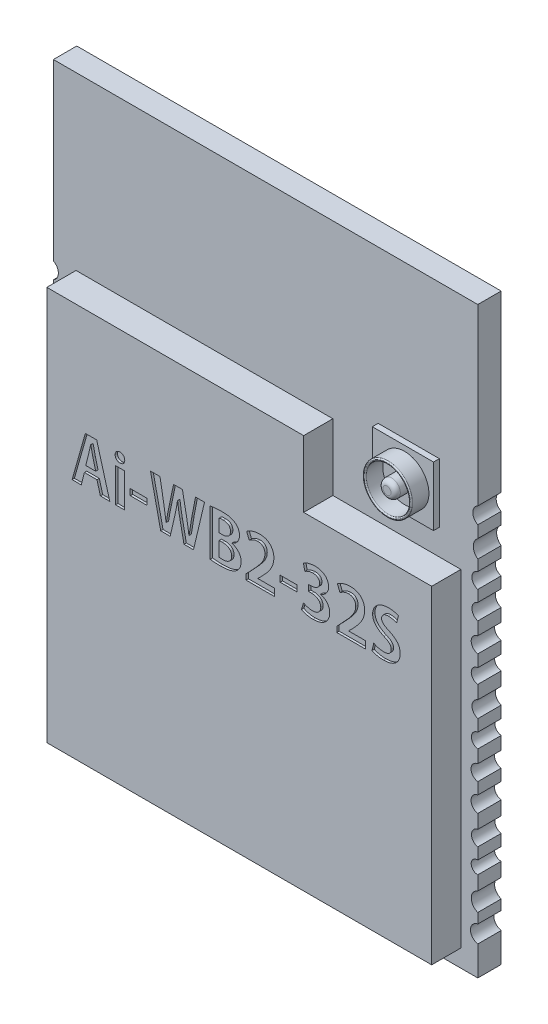
SolidWorks part; units mm, degrees
ref_plane "Plan de face" through (0, 0, 0) normal (0, 0, 1) x (1, 0, 0)
ref_plane "Plan de dessus" through (0, 0, 0) normal (0, 1, 0) x (1, 0, 0)
ref_plane "Plan de droite" through (0, 0, 0) normal (1, 0, 0) x (0, 0, -1)
sketch "fond pcb" plane through (0, 0, 0) normal (0, 0, 1) x (1, 0, 0)
  line L0 (-9.7255, 13.6033) -> (8.2745, 13.6033) construction
  line L1 (-9.8109, 5.5285) -> (-9.8109, 5.0184)
  line L2 (-9.8109, 13.6929) -> (8.3506, 13.6929)
  line L3 (-9.8109, 13.6929) -> (-9.8109, 6.2298)
  line L4 (-9.8109, -11.2676) -> (-7.3552, -11.2676)
  line L5 (8.3506, 13.6929) -> (8.3506, 6.2298)
  line L6 (-9.8109, -10.0063) -> (-9.8109, -11.2676)
  line L7 (-9.8109, -8.8368) -> (-9.8109, -9.2672)
  line L8 (-9.8109, -7.4423) -> (-9.8109, -8.0432)
  line L9 (-9.8109, -6.4072) -> (-9.8109, -6.8952)
  line L10 (-9.8109, -5.1671) -> (-9.8109, -5.7589)
  line L11 (-9.8109, -3.9896) -> (-9.8109, -4.4853)
  line L12 (-9.8109, -2.7786) -> (-9.8109, -3.3276)
  line L13 (-9.8109, -1.6551) -> (-9.8109, -2.1557)
  line L14 (-9.8109, -0.3849) -> (-9.8109, -0.9564)
  line L15 (-9.8109, 0.746) -> (-9.8109, 0.2321)
  line L16 (-9.8109, 1.9677) -> (-9.8109, 1.4147)
  line L17 (-9.8109, 3.1364) -> (-9.8109, 2.6533)
  line L18 (-9.8109, 4.2588) -> (-9.8109, 3.7971)
  line L19 (-0.7302, -11.2676) -> (-0.7302, -15.4653) construction
  line L20 (8.3506, 5.5285) -> (8.3506, 5.0184)
  line L21 (8.3506, 4.2588) -> (8.3506, 3.7971)
  line L22 (8.3506, 3.1364) -> (8.3506, 2.6533)
  line L23 (8.3506, 1.9677) -> (8.3506, 1.4147)
  line L24 (8.3506, 0.746) -> (8.3506, 0.2321)
  line L25 (8.3506, -0.3849) -> (8.3506, -0.9564)
  line L26 (8.3506, -1.6551) -> (8.3506, -2.1557)
  line L27 (8.3506, -2.7786) -> (8.3506, -3.3276)
  line L28 (8.3506, -3.9896) -> (8.3506, -4.4853)
  line L29 (8.3506, -5.1671) -> (8.3506, -5.7589)
  line L30 (8.3506, -6.4072) -> (8.3506, -6.8952)
  line L31 (8.3506, -7.4423) -> (8.3506, -8.0432)
  line L32 (8.3506, -8.8368) -> (8.3506, -9.2672)
  line L33 (8.3506, -10.0063) -> (8.3506, -11.2676)
  line L34 (6.0933, -11.2676) -> (8.3506, -11.2676)
  line L35 (3.3603, -11.2676) -> (4.0183, -11.2676)
  line L36 (1.8957, -11.2676) -> (2.5651, -11.2676)
  line L37 (0.5089, -11.2676) -> (1.1767, -11.2676)
  line L38 (-6.631, -11.2676) -> (-5.9558, -11.2676)
  line L39 (-5.1425, -11.2676) -> (-4.5122, -11.2676)
  line L40 (-3.7239, -11.2676) -> (-3.0992, -11.2676)
  line L41 (-0.9286, -11.2676) -> (-0.2711, -11.2676)
  line L42 (-1.7181, -11.2676) -> (-2.313, -11.2695)
  line L43 (-2.313, -11.2695) -> (-2.3158, -11.2585)
  line L44 (4.7334, -11.2676) -> (5.4735, -11.2631)
  arc A0 (-9.8109, 6.2298) -> (-9.8109, 5.5285) centre (-9.9945, 5.8791) cw
  arc A1 (-9.8109, 5.0184) -> (-9.8109, 4.2588) centre (-10.0892, 4.6386) cw
  arc A2 (-9.8109, 3.7971) -> (-9.8109, 3.1364) centre (-9.8997, 3.4667) cw
  arc A3 (-9.8109, 2.6533) -> (-9.8109, 1.9677) centre (-9.9208, 2.3105) cw
  arc A4 (-9.8109, 1.4147) -> (-9.8109, 0.746) centre (-9.8673, 1.0804) cw
  arc A5 (-9.8109, 0.2321) -> (-9.8109, -0.3849) centre (-9.8408, -0.0764) cw
  arc A6 (-9.8109, -0.9564) -> (-9.8109, -1.6551) centre (-9.9342, -1.3057) cw
  arc A7 (-9.8109, -2.1557) -> (-9.8109, -2.7786) centre (-9.8506, -2.4671) cw
  arc A8 (-9.8109, -3.3276) -> (-9.8109, -3.9896) centre (-9.8572, -3.6586) cw
  arc A9 (-9.8109, -4.4853) -> (-9.8109, -5.1671) centre (-9.8672, -4.8262) cw
  arc A10 (-9.8109, -5.7589) -> (-9.8109, -6.4072) centre (-9.8695, -6.083) cw
  arc A11 (-9.8109, -6.8952) -> (-9.8109, -7.4423) centre (-9.8024, -7.1687) cw
  arc A12 (-9.8109, -8.0432) -> (-9.8109, -8.8368) centre (-9.9522, -8.44) cw
  arc A13 (-9.8109, -9.2672) -> (-9.8109, -10.0063) centre (-9.873, -9.6368) cw
  arc A14 (8.3506, -9.2672) -> (8.3506, -10.0063) centre (8.4127, -9.6368) ccw
  arc A15 (8.3506, -8.0432) -> (8.3506, -8.8368) centre (8.4919, -8.44) ccw
  arc A16 (8.3506, -6.8952) -> (8.3506, -7.4423) centre (8.3421, -7.1687) ccw
  arc A17 (8.3506, -5.7589) -> (8.3506, -6.4072) centre (8.4091, -6.083) ccw
  arc A18 (8.3506, -4.4853) -> (8.3506, -5.1671) centre (8.4069, -4.8262) ccw
  arc A19 (8.3506, -3.3276) -> (8.3506, -3.9896) centre (8.3969, -3.6586) ccw
  arc A20 (8.3506, -2.1557) -> (8.3506, -2.7786) centre (8.3903, -2.4671) ccw
  arc A21 (8.3506, -0.9564) -> (8.3506, -1.6551) centre (8.4739, -1.3057) ccw
  arc A22 (8.3506, 0.2321) -> (8.3506, -0.3849) centre (8.3805, -0.0764) ccw
  arc A23 (8.3506, 1.4147) -> (8.3506, 0.746) centre (8.407, 1.0804) ccw
  arc A24 (8.3506, 2.6533) -> (8.3506, 1.9677) centre (8.4605, 2.3105) ccw
  arc A25 (8.3506, 3.7971) -> (8.3506, 3.1364) centre (8.4394, 3.4667) ccw
  arc A26 (8.3506, 5.0184) -> (8.3506, 4.2588) centre (8.6289, 4.6386) ccw
  arc A27 (8.3506, 6.2298) -> (8.3506, 5.5285) centre (8.5341, 5.8791) ccw
  arc A28 (-7.3552, -11.2676) -> (-6.631, -11.2676) centre (-6.9931, -11.3675) cw
  arc A29 (-5.9558, -11.2676) -> (-5.1425, -11.2676) centre (-5.5492, -11.4378) cw
  arc A30 (-4.5122, -11.2676) -> (-3.7239, -11.2676) centre (-4.118, -11.4414) cw
  arc A31 (-3.0992, -11.2676) -> (-2.3158, -11.2585) centre (-2.7054, -11.4475) cw
  arc A32 (-1.7181, -11.2676) -> (-0.9286, -11.2676) centre (-1.3234, -11.4346) cw
  arc A33 (-0.2711, -11.2676) -> (0.5089, -11.2676) centre (0.1189, -11.4428) cw
  arc A34 (1.1767, -11.2676) -> (1.8957, -11.2676) centre (1.5362, -11.3912) cw
  arc A35 (2.5651, -11.2676) -> (3.3603, -11.2676) centre (2.9627, -11.4378) cw
  arc A36 (4.0183, -11.2676) -> (4.7334, -11.2676) centre (4.3759, -11.3912) cw
  arc A37 (5.4735, -11.2631) -> (6.0933, -11.2676) centre (5.783, -11.3225) cw
  dimension "D1" = 18
sketch "shield alu" plane through (0, 0, 0) normal (0, 0, 1) x (1, 0, 0)
  line L1 (-8.8418, 6.3583) -> (2.1481, 6.3583)
  line L2 (-8.8418, 6.3583) -> (-8.8418, -10.5179)
  line L3 (-8.8418, -10.5179) -> (7.627, -10.5179)
  line L4 (7.627, 3.5134) -> (7.627, -10.5179)
  line L6 (2.1481, 6.3583) -> (2.1481, 3.5134)
  line L7 (2.1481, 3.5134) -> (7.627, 3.5134)
sketch "coaxcadre" plane through (0, 0, 0) normal (0, 0, 1) x (1, 0, 0)
  line L1 (4.0862, 7.1572) -> (6.7041, 7.1572)
  line L2 (4.0862, 7.1572) -> (4.0862, 4.6136)
  line L3 (4.0862, 4.6136) -> (6.7041, 4.6136)
  line L4 (6.7041, 7.1572) -> (6.7041, 4.6136)
sketch "coad reflief" plane through (0, 0, 0) normal (0, 0, 1) x (1, 0, 0)
  circle A0 centre (5.4663, 5.8545) radius 0.3694
  circle A1 centre (5.4663, 5.8916) radius 0.9336
  circle A2 centre (5.4663, 5.8916) radius 1.0425
extrude "Boss.-Extru.1" add sketch "fond pcb" against normal blind 1
extrude "Boss.-Extru.2" add sketch "shield alu" along normal blind 1.25
extrude "Boss.-Extru.3" add sketch "coaxcadre" along normal blind 0.25
extrude "Boss.-Extru.5" add sketch "coad reflief" along normal blind 1 contours A2 A1 | A0
fillet "Congé1" radius 0.05 2 edges at (6.3999, 5.8916, 1) (6.5088, 5.8916, 1)
fillet "Congé2" radius 0.2 1 edges at (5.8357, 5.8545, 1)
sketch "Esquisse7" plane through (0, 0, 1.25) normal (0, 0, 1) x (1, 0, 0)
  text T0 "Ai-WB2-32S" font "@Adobe Gothic Std B" height 2
extrude "Enlèv. mat.-Extru.1" cut sketch "Esquisse7" against normal blind 0.1
